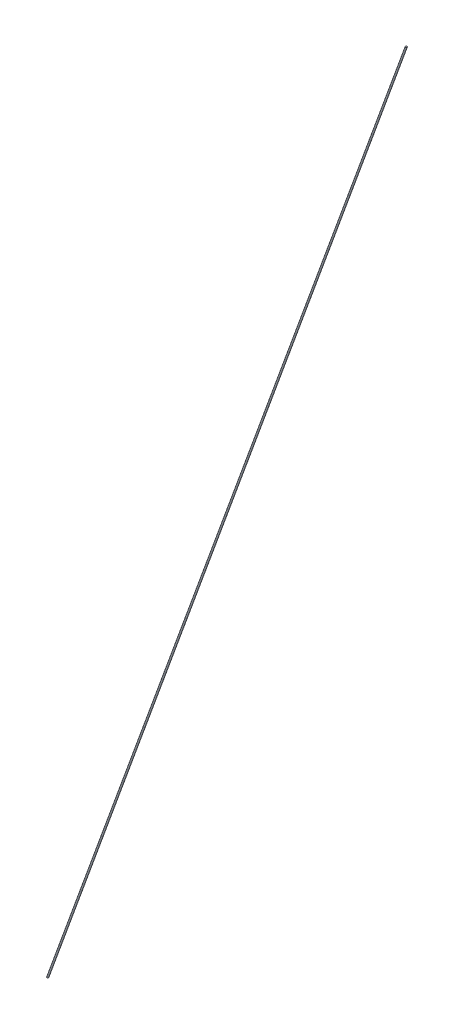
SolidWorks part; units mm, degrees
ref_plane "Front Plane" through (0, 0, 0) normal (0, 0, 1) x (1, 0, 0)
ref_plane "Top Plane" through (0, 0, 0) normal (0, 1, 0) x (1, 0, 0)
ref_plane "Right Plane" through (0, 0, 0) normal (1, 0, 0) x (0, 0, -1)
sketch "Sketch1" plane through (0, 0, 0) normal (0, 0, 1) x (1, 0, 0)
  line L0 (54.3711, 298.3782) -> (-30.9049, 64.0843)
  line L1 (-30.9049, 64.0843) -> (-30.7049, 64.0843)
  line L2 (-30.7049, 64.0843) -> (54.5711, 298.3782)
  line L3 (54.5711, 298.3782) -> (54.3711, 298.3782)
  point P4 (-30.8049, 64.0843)
  dimension "D2" = 0.2
revolve "Revolve1" add sketch "Sketch1" angle 360 about L2
